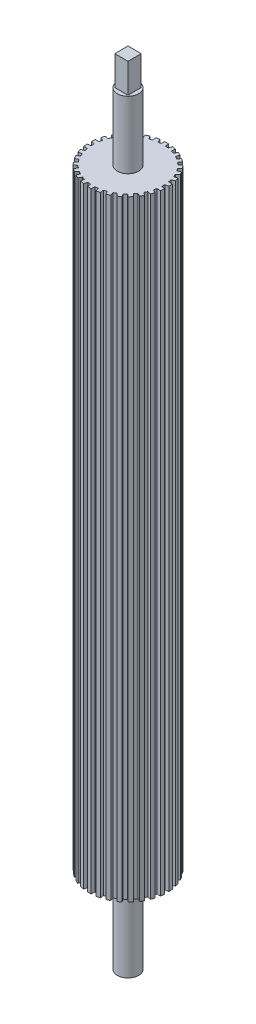
SolidWorks part; units mm, degrees
ref_plane "Front Plane" through (0, 0, 0) normal (0, 0, 1) x (1, 0, 0)
ref_plane "Top Plane" through (0, 0, 0) normal (0, 1, 0) x (1, 0, 0)
ref_plane "Right Plane" through (0, 0, 0) normal (1, 0, 0) x (0, 0, -1)
sketch "Sketch2" plane through (0, 0, 0) normal (0, 1, 0) x (1, 0, 0)
  line L1 (-0.7753, 12.6763) -> (-0.6703, 13.9539)
  line L2 (0.7753, 12.6763) -> (0.6703, 13.9539)
  line L3 (1.8772, 12.5605) -> (2.2456, 13.7883)
  line L4 (3.3939, 12.2381) -> (3.5568, 13.5096)
  line L5 (4.4476, 11.8957) -> (5.0633, 13.0201)
  line L6 (5.8642, 11.265) -> (6.2879, 12.4749)
  line L7 (6.8237, 10.7111) -> (7.6597, 11.6829)
  line L8 (8.0782, 9.7996) -> (8.7442, 10.895)
  line L9 (8.9015, 9.0583) -> (9.9213, 9.8351)
  line L10 (9.9391, 7.9059) -> (10.8183, 8.8389)
  line L11 (10.5903, 7.0096) -> (11.7493, 7.5574)
  line L12 (11.3657, 5.6667) -> (12.4196, 6.3965)
  line L13 (11.8163, 4.6546) -> (13.0638, 4.9494)
  line L14 (12.2955, 3.1798) -> (13.4781, 3.6745)
  line L15 (12.5258, 2.0961) -> (13.8074, 2.1252)
  line L16 (12.6879, 0.554) -> (13.9475, 0.792)
  line L17 (12.6879, -0.554) -> (13.9475, -0.792)
  line L18 (12.5258, -2.0961) -> (13.8074, -2.1252)
  line L19 (12.2955, -3.1798) -> (13.4781, -3.6745)
  line L20 (11.8163, -4.6546) -> (13.0638, -4.9494)
  line L21 (11.3657, -5.6667) -> (12.4196, -6.3965)
  line L22 (10.5903, -7.0096) -> (11.7493, -7.5574)
  line L23 (9.9391, -7.9059) -> (10.8183, -8.8389)
  line L24 (8.9015, -9.0583) -> (9.9213, -9.8351)
  line L25 (8.0782, -9.7996) -> (8.7442, -10.895)
  line L26 (6.8237, -10.7111) -> (7.6597, -11.6829)
  line L27 (5.8642, -11.265) -> (6.2879, -12.4749)
  line L28 (4.4476, -11.8957) -> (5.0633, -13.0201)
  line L29 (3.3939, -12.2381) -> (3.5568, -13.5096)
  line L30 (1.8772, -12.5605) -> (2.2456, -13.7883)
  line L31 (0.7753, -12.6763) -> (0.6703, -13.9539)
  line L32 (-0.7753, -12.6763) -> (-0.6703, -13.9539)
  line L33 (-1.8772, -12.5605) -> (-2.2456, -13.7883)
  line L34 (-3.3939, -12.2381) -> (-3.5568, -13.5096)
  line L35 (-4.4476, -11.8957) -> (-5.0633, -13.0201)
  line L36 (-5.8642, -11.265) -> (-6.2879, -12.4749)
  line L37 (-6.8237, -10.7111) -> (-7.6597, -11.6829)
  line L38 (-8.0782, -9.7996) -> (-8.7442, -10.895)
  line L39 (-8.9015, -9.0583) -> (-9.9213, -9.8351)
  line L40 (-9.9391, -7.9059) -> (-10.8183, -8.8389)
  line L41 (-10.5903, -7.0096) -> (-11.7493, -7.5574)
  line L42 (-11.3657, -5.6667) -> (-12.4196, -6.3965)
  line L43 (-11.8163, -4.6546) -> (-13.0638, -4.9494)
  line L44 (-12.2955, -3.1798) -> (-13.4781, -3.6745)
  line L45 (-12.5258, -2.0961) -> (-13.8074, -2.1252)
  line L46 (-12.6879, -0.554) -> (-13.9475, -0.792)
  line L47 (-12.6879, 0.554) -> (-13.9475, 0.792)
  line L48 (-12.5258, 2.0961) -> (-13.8074, 2.1252)
  line L49 (-12.2955, 3.1798) -> (-13.4781, 3.6745)
  line L50 (-11.8163, 4.6546) -> (-13.0638, 4.9494)
  line L51 (-11.3657, 5.6667) -> (-12.4196, 6.3965)
  line L52 (-10.5903, 7.0096) -> (-11.7493, 7.5574)
  line L53 (-9.9391, 7.9059) -> (-10.8183, 8.8389)
  line L54 (-8.9015, 9.0583) -> (-9.9213, 9.8351)
  line L55 (-8.0782, 9.7996) -> (-8.7442, 10.895)
  line L56 (-6.8237, 10.7111) -> (-7.6597, 11.6829)
  line L57 (-5.8642, 11.265) -> (-6.2879, 12.4749)
  line L58 (-4.4476, 11.8957) -> (-5.0633, 13.0201)
  line L59 (-3.3939, 12.2381) -> (-3.5568, 13.5096)
  line L60 (-1.8772, 12.5605) -> (-2.2456, 13.7883)
  arc A0 (-2.2456, 13.7883) -> (-3.5568, 13.5096) centre (0, 0) ccw
  arc A1 (-0.7753, 12.6763) -> (-1.8772, 12.5605) centre (0, 0) ccw
  arc A3 (-3.3939, 12.2381) -> (-4.4476, 11.8957) centre (0, 0) ccw
  arc A4 (-5.0633, 13.0201) -> (-6.2879, 12.4749) centre (0, 0) ccw
  arc A5 (-5.8642, 11.265) -> (-6.8237, 10.7111) centre (0, 0) ccw
  arc A6 (-7.6597, 11.6829) -> (-8.7442, 10.895) centre (0, 0) ccw
  arc A7 (-8.0782, 9.7996) -> (-8.9015, 9.0583) centre (0, 0) ccw
  arc A8 (-9.9213, 9.8351) -> (-10.8183, 8.8389) centre (0, 0) ccw
  arc A9 (-9.9391, 7.9059) -> (-10.5903, 7.0096) centre (0, 0) ccw
  arc A10 (-11.7493, 7.5574) -> (-12.4196, 6.3965) centre (0, 0) ccw
  arc A11 (-11.3657, 5.6667) -> (-11.8163, 4.6546) centre (0, 0) ccw
  arc A12 (-13.0638, 4.9494) -> (-13.4781, 3.6745) centre (0, 0) ccw
  arc A13 (-12.2955, 3.1798) -> (-12.5258, 2.0961) centre (0, 0) ccw
  arc A14 (-13.8074, 2.1252) -> (-13.9475, 0.792) centre (0, 0) ccw
  arc A15 (-12.6879, 0.554) -> (-12.6879, -0.554) centre (0, 0) ccw
  arc A16 (-13.9475, -0.792) -> (-13.8074, -2.1252) centre (0, 0) ccw
  arc A17 (-12.5258, -2.0961) -> (-12.2955, -3.1798) centre (0, 0) ccw
  arc A18 (-13.4781, -3.6745) -> (-13.0638, -4.9494) centre (0, 0) ccw
  arc A19 (-11.8163, -4.6546) -> (-11.3657, -5.6667) centre (0, 0) ccw
  arc A20 (-12.4196, -6.3965) -> (-11.7493, -7.5574) centre (0, 0) ccw
  arc A21 (-10.5903, -7.0096) -> (-9.9391, -7.9059) centre (0, 0) ccw
  arc A22 (-10.8183, -8.8389) -> (-9.9213, -9.8351) centre (0, 0) ccw
  arc A23 (-8.9015, -9.0583) -> (-8.0782, -9.7996) centre (0, 0) ccw
  arc A24 (-8.7442, -10.895) -> (-7.6597, -11.6829) centre (0, 0) ccw
  arc A25 (-6.8237, -10.7111) -> (-5.8642, -11.265) centre (0, 0) ccw
  arc A26 (-6.2879, -12.4749) -> (-5.0633, -13.0201) centre (0, 0) ccw
  arc A27 (-4.4476, -11.8957) -> (-3.3939, -12.2381) centre (0, 0) ccw
  arc A28 (-3.5568, -13.5096) -> (-2.2456, -13.7883) centre (0, 0) ccw
  arc A29 (-1.8772, -12.5605) -> (-0.7753, -12.6763) centre (0, 0) ccw
  arc A30 (-0.6703, -13.9539) -> (0.6703, -13.9539) centre (0, 0) ccw
  arc A31 (0.7753, -12.6763) -> (1.8772, -12.5605) centre (0, 0) ccw
  arc A32 (2.2456, -13.7883) -> (3.5568, -13.5096) centre (0, 0) ccw
  arc A33 (3.3939, -12.2381) -> (4.4476, -11.8957) centre (0, 0) ccw
  arc A34 (5.0633, -13.0201) -> (6.2879, -12.4749) centre (0, 0) ccw
  arc A35 (5.8642, -11.265) -> (6.8237, -10.7111) centre (0, 0) ccw
  arc A36 (7.6597, -11.6829) -> (8.7442, -10.895) centre (0, 0) ccw
  arc A37 (8.0782, -9.7996) -> (8.9015, -9.0583) centre (0, 0) ccw
  arc A38 (9.9213, -9.8351) -> (10.8183, -8.8389) centre (0, 0) ccw
  arc A39 (9.9391, -7.9059) -> (10.5903, -7.0096) centre (0, 0) ccw
  arc A40 (11.7493, -7.5574) -> (12.4196, -6.3965) centre (0, 0) ccw
  arc A41 (11.3657, -5.6667) -> (11.8163, -4.6546) centre (0, 0) ccw
  arc A42 (13.0638, -4.9494) -> (13.4781, -3.6745) centre (0, 0) ccw
  arc A43 (12.2955, -3.1798) -> (12.5258, -2.0961) centre (0, 0) ccw
  arc A44 (13.8074, -2.1252) -> (13.9475, -0.792) centre (0, 0) ccw
  arc A45 (12.6879, -0.554) -> (12.6879, 0.554) centre (0, 0) ccw
  arc A46 (13.9475, 0.792) -> (13.8074, 2.1252) centre (0, 0) ccw
  arc A47 (12.5258, 2.0961) -> (12.2955, 3.1798) centre (0, 0) ccw
  arc A48 (13.4781, 3.6745) -> (13.0638, 4.9494) centre (0, 0) ccw
  arc A49 (0.6703, 13.9539) -> (-0.6703, 13.9539) centre (0, 0) ccw
  arc A50 (3.5568, 13.5096) -> (2.2456, 13.7883) centre (0, 0) ccw
  arc A51 (6.2879, 12.4749) -> (5.0633, 13.0201) centre (0, 0) ccw
  arc A52 (8.7442, 10.895) -> (7.6597, 11.6829) centre (0, 0) ccw
  arc A53 (1.8772, 12.5605) -> (0.7753, 12.6763) centre (0, 0) ccw
  arc A54 (4.4476, 11.8957) -> (3.3939, 12.2381) centre (0, 0) ccw
  arc A55 (6.8237, 10.7111) -> (5.8642, 11.265) centre (0, 0) ccw
  arc A56 (8.9015, 9.0583) -> (8.0782, 9.7996) centre (0, 0) ccw
  arc A57 (10.5903, 7.0096) -> (9.9391, 7.9059) centre (0, 0) ccw
  arc A58 (10.8183, 8.8389) -> (9.9213, 9.8351) centre (0, 0) ccw
  arc A59 (12.4196, 6.3965) -> (11.7493, 7.5574) centre (0, 0) ccw
  arc A60 (11.8163, 4.6546) -> (11.3657, 5.6667) centre (0, 0) ccw
  point P129 (0, 0)
  dimension "D1" = 30
extrude "Boss-Extrude1" add sketch "Sketch2" along normal blind 211.1375 contours L39 A22 L40 A21 L41 A20 L42 A19 L43 A18 L44 A17 L45 A16 L46 A15 L47 A14 L48 A13 L49 A12 L50 A11 L51 A10 L52 A9 L53 A8 L54 A7 L55 A6 L56 A5 L57 A4 L58 A3 L59 A0 L60 A1 L1 A49 L2 A53 L3 A50 L4 A54 L5 A51 L6 A55 L7 A52 L8 A56 L9 A58 L10 A57 L11 A59 L12 A60 L13 A48 L14 A47 L15 A46 L16 A45 L17 A44 L18 A43 L19 A42 L20 A41 L21 A40 L22 A39 L23 A38 L24 A37 L25 A36 L26 A35 L27 A34 L28 A33 L29 A32 L30 A31 L31 A30 L32 A29 L33 A28 L34 A27 L35 A26 L36 A25 L37 A24 L38 A23
scale "Scale2" scale about centroid uniform scaling no x scale factor 0.96 y scale factor 1 z scale factor 0.96
sketch "Sketch3" plane through (0, 211.1375, 0) normal (0, 1, 0) x (1, 0, 0)
  circle A0 centre (0, 0) radius 3.6805
  dimension "D1" = 7.3609
extrude "Boss-Extrude2" add sketch "Sketch3" along normal blind 23.2093
sketch "Sketch4" plane through (0, 0, 0) normal (0, -1, 0) x (-1, 0, 0)
  circle A0 centre (0, 0) radius 3.6805
  dimension "D1" = 7.3609
extrude "Boss-Extrude3" add sketch "Sketch4" along normal blind 29.5593
sketch "Sketch6" plane through (0, 234.3467, 0) normal (0, 1, 0) x (1, 0, 0)
  line L1 (-2.286, -2.286) -> (2.286, -2.286)
  line L2 (-2.286, -2.286) -> (-2.286, 2.286)
  line L3 (-2.286, 2.286) -> (2.286, 2.286)
  line L4 (2.286, -2.286) -> (2.286, 2.286)
  line L9 (-2.286, -2.286) -> (2.286, 2.286) construction
  line L10 (-2.286, 2.286) -> (2.286, -2.286) construction
  point P0 (0, 0)
  dimension "D1" = 4.572
  dimension "D2" = 4.572
extrude "Boss-Extrude4" add sketch "Sketch6" along normal blind 10.16
